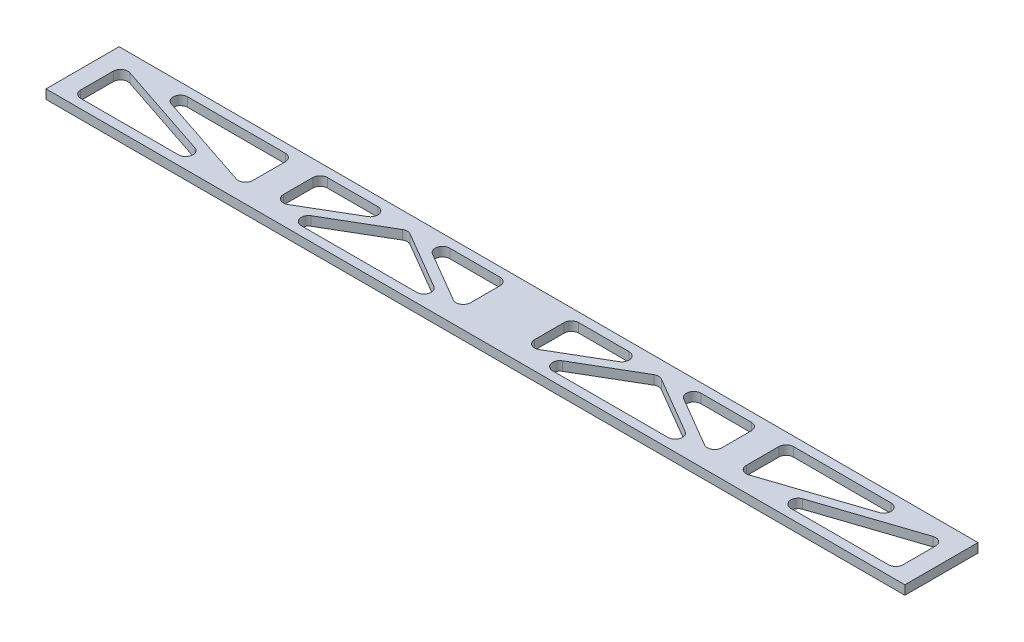
SolidWorks part; units mm, degrees
material "Balsa"
ref_plane "Front Plane" through (0, 0, 0) normal (0, 0, 1) x (1, 0, 0)
ref_plane "Top Plane" through (0, 0, 0) normal (0, 1, 0) x (1, 0, 0)
ref_plane "Right Plane" through (0, 0, 0) normal (1, 0, 0) x (0, 0, -1)
sketch "Sketch1" plane through (0, 0, 0) normal (0, 1, 0) x (1, 0, 0)
  line L1 (149.225, -12.7) -> (-149.225, -12.7)
  line L2 (149.225, -12.7) -> (149.225, 12.7)
  line L3 (149.225, 12.7) -> (-149.225, 12.7)
  line L4 (-149.225, -12.7) -> (-149.225, 12.7)
  point P0 (0, 12.7)
  point P6 (-149.225, 0)
  dimension "D1" = 25.4
  dimension "D2" = 298.45
extrude "Boss-Extrude1" add sketch "Sketch1" along normal blind 3.175
sketch "Sketch2" plane through (0, 3.175, 0) normal (0, 1, 0) x (1, 0, 0)
  line L0 (149.225, -12.7) -> (149.225, 12.7) construction
  line L2 (-149.225, 12.7) -> (-149.225, -12.7) construction
  line L4 (149.225, -12.7) -> (149.225, 12.7)
  line L6 (-149.225, 12.7) -> (-149.225, -12.7)
  line L8 (149.225, 9.525) -> (-149.225, 9.525)
  line L9 (-149.225, -9.525) -> (149.225, -9.525)
  line L10 (-142.875, 9.525) -> (-142.875, -9.525)
  line L11 (-80.9625, 9.525) -> (-80.9625, -9.525) construction
  line L12 (142.875, 9.525) -> (142.875, -9.525)
  line L13 (0, -9.525) -> (0, 9.525) construction
  line L14 (11.1125, 9.525) -> (11.1125, -9.525)
  line L15 (-11.1125, 9.525) -> (-11.1125, -9.525)
  line L16 (-85.725, 9.525) -> (-85.725, -9.525)
  line L17 (-76.2, 9.525) -> (-76.2, -9.525)
  line L18 (80.9625, 9.525) -> (80.9625, -9.525) construction
  line L19 (85.725, 9.525) -> (85.725, -9.525)
  line L20 (76.2, 9.525) -> (76.2, -9.525)
  line L21 (-76.2, -9.525) -> (-43.6562, 9.525)
  line L22 (-43.6562, 9.525) -> (-11.1125, -9.525)
  line L23 (-85.725, -9.525) -> (-142.875, 9.525)
  line L24 (11.1125, -9.525) -> (43.6562, 9.525)
  line L25 (43.6562, 9.525) -> (76.2, -9.525)
  line L26 (85.725, -9.525) -> (142.875, 9.525)
  line L27 (-85.223, -8.019) -> (-142.373, 11.031)
  line L28 (-75.398, -10.895) -> (-43.6562, 7.6855)
  line L29 (-43.6562, 7.6855) -> (-11.9145, -10.895)
  line L30 (11.9145, -10.895) -> (43.6562, 7.6855)
  line L31 (43.6562, 7.6855) -> (75.398, -10.895)
  line L32 (86.227, -11.031) -> (143.377, 8.019)
  line L33 (-86.227, -11.031) -> (-143.377, 8.019)
  line L34 (-77.002, -8.155) -> (-43.6562, 11.3645)
  line L35 (-43.6562, 11.3645) -> (-10.3105, -8.155)
  line L36 (10.3105, -8.155) -> (43.6562, 11.3645)
  line L37 (43.6562, 11.3645) -> (77.002, -8.155)
  line L38 (85.223, -8.019) -> (142.373, 11.031)
  dimension "D1" = 3.175
  dimension "D2" = 3.175
  dimension "D3" = 6.35
  dimension "D4" = 6.35
  dimension "D11" = 4.7625
  dimension "D12" = 4.7625
  dimension "D8" = 9.525
  dimension "D9" = 4.7625
  dimension "D7" = 63.5
  dimension "D10" = 63.5
  dimension "D5" = 22.225
  dimension "D6" = 11.1125
  dimension "D13" = 1.5875
  dimension "D14" = 1.5875
extrude "Cut-Extrude1" cut sketch "Sketch2" against normal through all contours L9 L33 L10 | L27 L16 L8 | L17 L34 L8 | L29 L28 L9 | L8 L35 L15 | L14 L36 L8 | L31 L30 L9 | L8 L37 L20 | L19 L38 L8 | L32 L9 L12
fillet "Fillet1" radius 2.54 30 edges at (-14.2549, 1.5875, 9.525) (-73.0576, 1.5875, 9.525) (-43.6562, 1.5875, -7.6855) (-11.1125, 1.5875, 7.6855) (-40.5138, 1.5875, -9.525) (-11.1125, 1.5875, -9.525) (-46.7987, 1.5875, -9.525) (-76.2, 1.5875, 7.6855) (-76.2, 1.5875, -9.525) (73.0576, 1.5875, 9.525) (14.2549, 1.5875, 9.525) (43.6562, 1.5875, -7.6855) (142.875, 1.5875, -7.8516) (142.875, 1.5875, 9.525) (90.7451, 1.5875, 9.525) (40.5138, 1.5875, -9.525) (11.1125, 1.5875, 7.6855) (11.1125, 1.5875, -9.525) (76.2, 1.5875, 7.6855) (46.7987, 1.5875, -9.525) (76.2, 1.5875, -9.525) (137.8549, 1.5875, -9.525) (85.725, 1.5875, 7.8516) (85.725, 1.5875, -9.525) (-137.8549, 1.5875, -9.525) (-85.725, 1.5875, 7.8516) (-85.725, 1.5875, -9.525) (-90.7451, 1.5875, 9.525) (-142.875, 1.5875, 9.525) (-142.875, 1.5875, -7.8516)
equation "\"D10@Sketch2\"=\"D7@Sketch2\""
equation "\"D6@Sketch2\"=\"D5@Sketch2\"/2"
